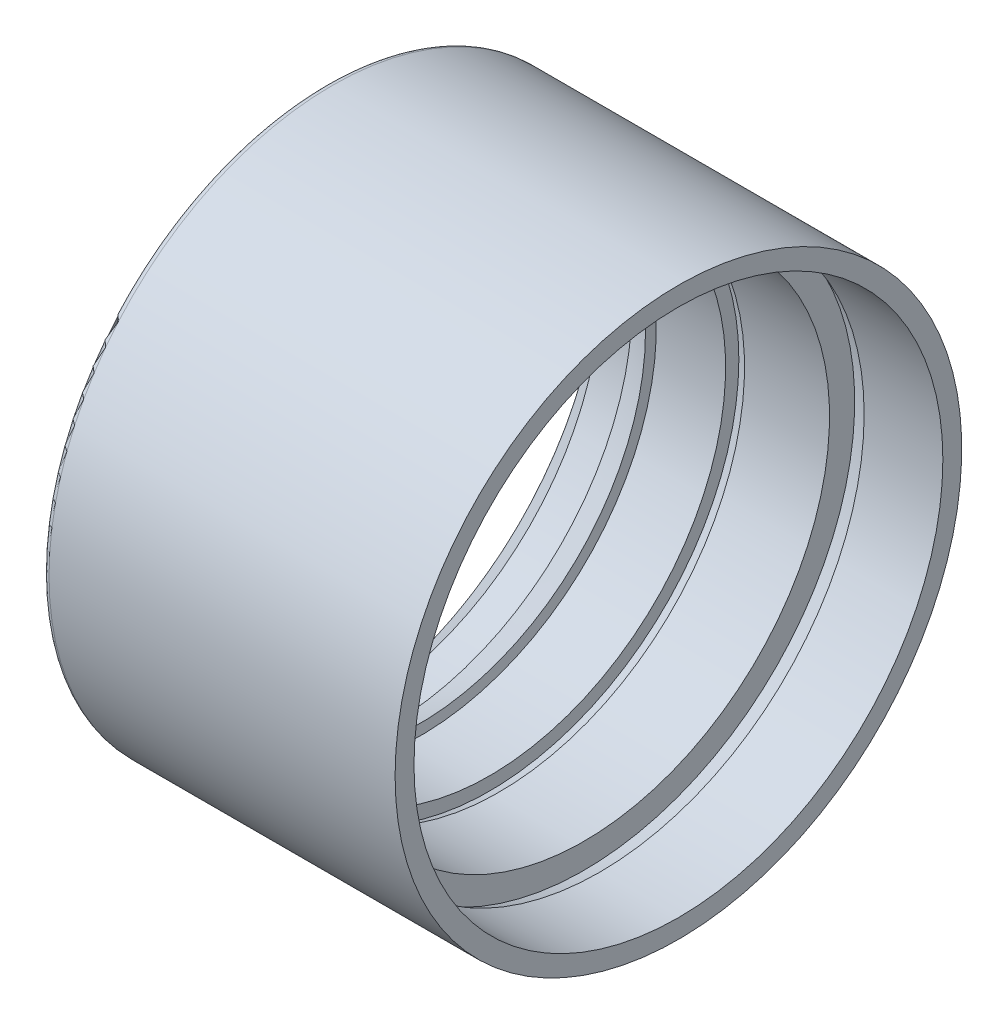
SolidWorks part; units mm, degrees
material "3.3535 (EN-AW 5754)"
ref_plane "Přední rovina" through (0, 0, 0) normal (0, 0, 1) x (1, 0, 0)
ref_plane "Horní rovina" through (0, 0, 0) normal (0, 1, 0) x (1, 0, 0)
ref_plane "Pravá rovina" through (0, 0, 0) normal (1, 0, 0) x (0, 0, -1)
sketch "Skica1" plane through (0, 0, 0) normal (0, 0, 1) x (1, 0, 0)
  line L0 (0, 0) -> (99.6753, 0) construction
  line L1 (-41.2266, 36) -> (-45.875, 38.5)
  line L2 (-45.875, 38.5) -> (-50.875, 38.5)
  line L4 (-57.375, 45) -> (0, 45)
  line L5 (0, 45) -> (0, 42)
  line L6 (0, 42) -> (-12.5, 42)
  line L7 (-12.5, 42) -> (-15, 43)
  line L8 (-15, 43) -> (-15, 39)
  line L9 (-15, 39) -> (-28.5, 39)
  line L10 (-28.5, 39) -> (-30, 39.6)
  line L11 (-30, 39.6) -> (-30, 37.5)
  line L12 (-30, 37.5) -> (-41, 37.5)
  line L13 (-50.875, 38.5) -> (-57.375, 45)
  arc A0 (-41.2266, 36) -> (-41, 37.5) centre (202.125, 0) cw
  arc A1 (-43.875, 0) -> (-41, 37.5) centre (202.125, 0) cw construction
  dimension "D1" = 246
  dimension "D2" = 1.5
  dimension "D3" = 37.5
  dimension "D4" = 38.5
  dimension "D5" = 2
  dimension "D6" = 11
  dimension "D7" = 0.6
  dimension "D8" = 1.5
  dimension "D9" = 15
  dimension "D10" = 15
  dimension "D11" = 3
  dimension "D12" = 5
  dimension "D13" = 45
  dimension "D14" = 39
  dimension "D15" = 1
  dimension "D16" = 42
revolve "Rotovat1" add sketch "Skica1" angle 360 about L0
cosmetic thread "Kosmetický závit1" parameters "D2"=100.33
fillet "Zaoblit1" radius 1 1 edges at (-57.375, 0, 45)
thread "Závit1" pitch 1 start angle 0, offset 0, length 0, pitch 1, diameter 78
ref_plane "Rovina1" through (-50.875, 0, -39) normal (0, -1, 0) x (0, 0, -1)
sketch "Profil závitu1" plane through (-50.875, 0, -39) normal (0, -1, 0) x (0, 0, -1)
  line L0 (0, 0) -> (0, 1) construction
  line L11 (0, 0) -> (0, 0.875)
  line L12 (0, 0.875) -> (-0.5413, 0.5625)
  line L13 (-0.5413, 0.5625) -> (-0.5413, 0.3125)
  line L15 (-0.5413, 0.3125) -> (0, 0)
  line L17 (-0.5413, 0.4375) -> (0, 0.4375) construction
  point P2 (0, 0)
  dimension "Pitch" = 1
  dimension "Profile_Angle" = 60
  dimension "Profile_Land" = 0.25
  dimension "Profile_Height" = 0.5413
thread "Závit3" pitch 1 start angle 0, offset 0, length 0, pitch 1, diameter 78
ref_plane "Rovina4" through (-15, 0, 39) normal (0, -1, 0) x (0, 0, 1)
sketch "Profil závitu4" plane through (-15, 0, 39) normal (0, -1, 0) x (0, 0, 1)
  line L0 (0, 0) -> (0, 1) construction
  line L1 (0, 0) -> (0.5413, 0.3125)
  line L2 (0.5413, 0.3125) -> (0.5413, 0.4375)
  line L3 (0.5413, 0.4375) -> (0, 0.75)
  line L4 (0.5413, 0.375) -> (0, 0.375) construction
  line L11 (0, 0) -> (0, 0.75)
  point P2 (0, 0)
  dimension "Pitch" = 1
  dimension "Profile_Angle" = 60
  dimension "Profile_Land" = 0.125
  dimension "Profile_Height" = 0.5413
thread "Závit4" pitch 1 start angle 0, offset 0, length 0, pitch 1, diameter 84
ref_plane "Rovina5" through (0, 0, 42) normal (0, -1, 0) x (0, 0, 1)
sketch "Profil závitu5" plane through (0, 0, 42) normal (0, -1, 0) x (0, 0, 1)
  line L0 (0, 0) -> (0, 1) construction
  line L1 (0, 0) -> (0.5413, 0.3125)
  line L2 (0.5413, 0.3125) -> (0.5413, 0.4375)
  line L3 (0.5413, 0.4375) -> (0, 0.75)
  line L4 (0.5413, 0.375) -> (0, 0.375) construction
  line L11 (0, 0) -> (0, 0.75)
  point P2 (0, 0)
  dimension "Pitch" = 1
  dimension "Profile_Angle" = 60
  dimension "Profile_Land" = 0.125
  dimension "Profile_Height" = 0.5413
